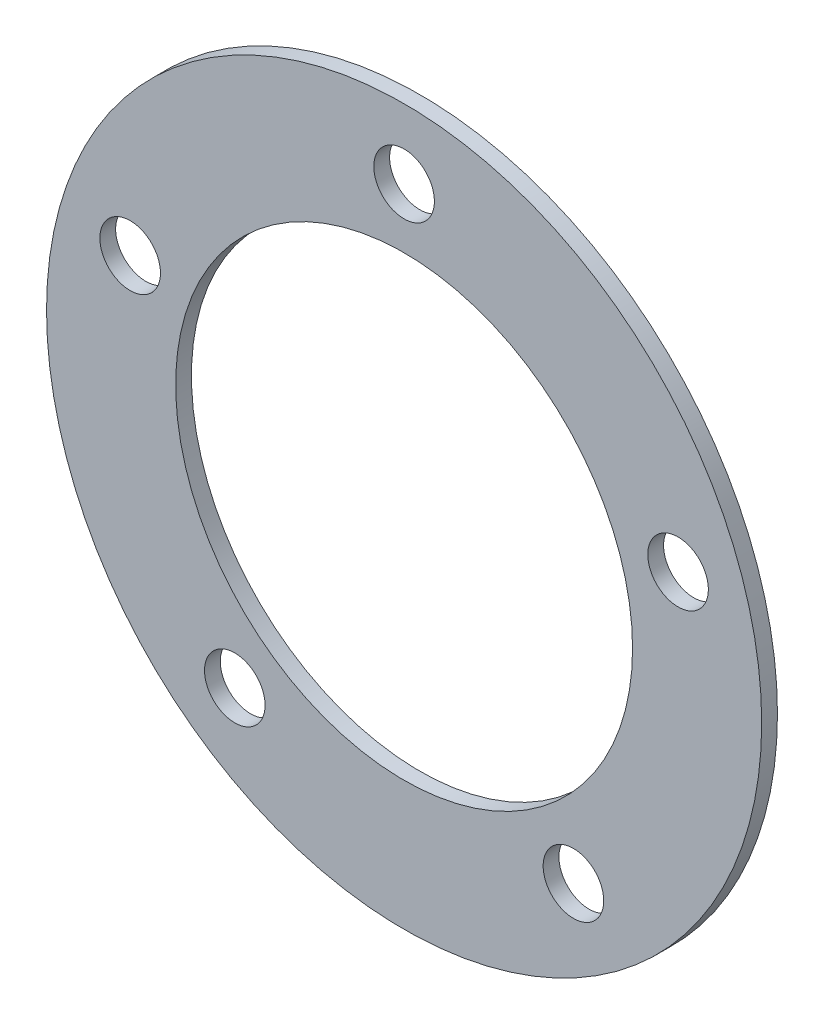
SolidWorks part; units mm, degrees
ref_plane "Front Plane" through (0, 0, 0) normal (0, 0, 1) x (1, 0, 0)
ref_plane "Top Plane" through (0, 0, 0) normal (0, 1, 0) x (1, 0, 0)
ref_plane "Right Plane" through (0, 0, 0) normal (1, 0, 0) x (0, 0, -1)
sketch "Sketch1" plane through (0, 0, 0) normal (0, 0, 1) x (1, 0, 0)
  line L0 (0, 14.5) -> (0, 0) construction
  line L1 (0, 0) -> (13.7903, 4.4807) construction
  line L3 (8.5229, -11.7307) -> (0, 0) construction
  line L4 (0, 0) -> (-8.5229, -11.7307) construction
  line L6 (-13.7903, 4.4807) -> (0, 0) construction
  circle A0 centre (0, 0) radius 11.5
  circle A1 centre (0, 0) radius 18
  circle A2 centre (0, 0) radius 14.5 construction
  circle A3 centre (0, 14.5) radius 1.525
  circle A4 centre (13.7903, 4.4807) radius 1.525
  circle A5 centre (8.5229, -11.7307) radius 1.525
  circle A6 centre (-8.5229, -11.7307) radius 1.525
  circle A7 centre (-13.7903, 4.4807) radius 1.525
  dimension "D1" = 29
  dimension "D2" = 23
  dimension "D3" = 36
  dimension "D8" = 3.05
  dimension "D4" = 72
  dimension "D5" = 72
  dimension "D6" = 72
  dimension "D7" = 72
extrude "Boss-Extrude1" add sketch "Sketch1" along normal blind 0.7937
